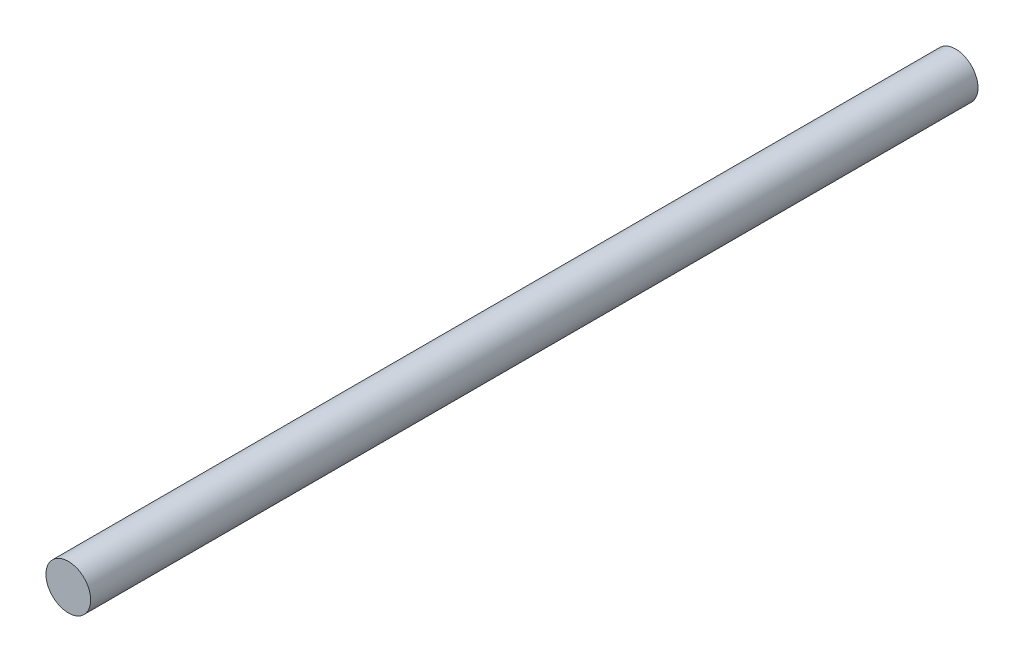
SolidWorks part; units mm, degrees
material "6061-T6 (SS)"
ref_plane "Front Plane" through (0, 0, 0) normal (0, 0, 1) x (1, 0, 0)
ref_plane "Top Plane" through (0, 0, 0) normal (0, 1, 0) x (1, 0, 0)
ref_plane "Right Plane" through (0, 0, 0) normal (1, 0, 0) x (0, 0, -1)
sketch "Sketch1" plane through (0, 0, 0) normal (0, 0, 1) x (1, 0, 0)
  circle A0 centre (0, 0) radius 3.175
  dimension "D1" = 6.35
extrude "Boss-Extrude1" add sketch "Sketch1" along normal blind 126 contours A0
